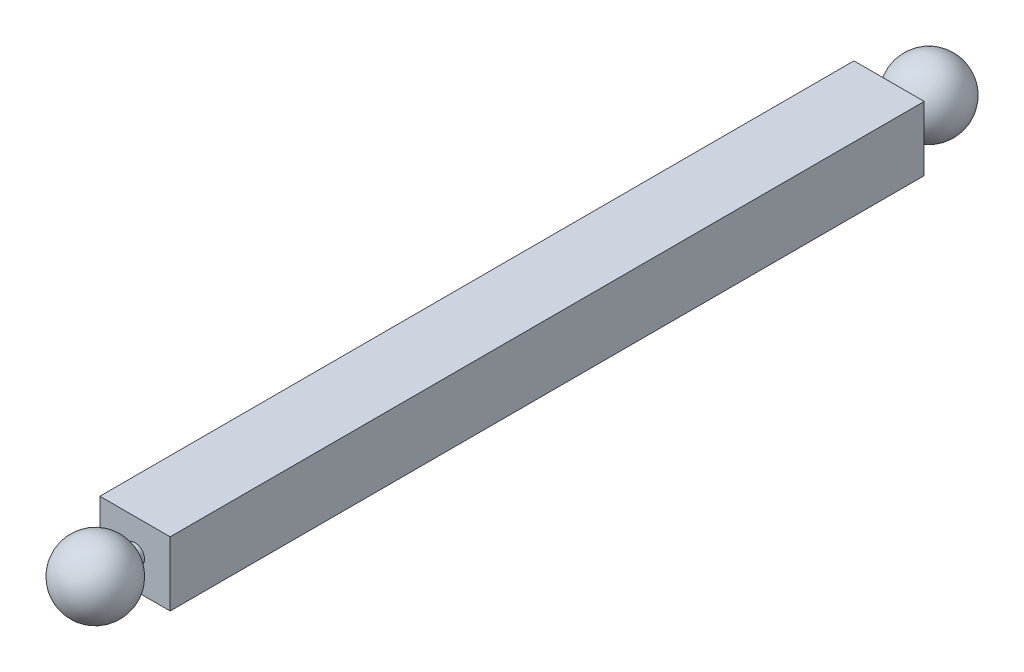
SolidWorks part; units mm, degrees
ref_plane "前视基准面" through (0, 0, 0) normal (0, 0, 1) x (1, 0, 0)
ref_plane "上视基准面" through (0, 0, 0) normal (0, 1, 0) x (1, 0, 0)
ref_plane "右视基准面" through (0, 0, 0) normal (1, 0, 0) x (0, 0, -1)
sketch "草图1" plane through (0, 0, 0) normal (0, 0, 1) x (1, 0, 0)
  line L0 (-8.5103, -3.5207) -> (-12.5103, -7.5207)
  line L1 (-12.5103, -3.5207) -> (-8.5103, -3.5207)
  line L2 (-12.5103, -3.5207) -> (-12.5103, -7.5207)
  line L3 (-12.5103, -7.5207) -> (-8.5103, -7.5207)
  line L4 (-8.5103, -3.5207) -> (-8.5103, -7.5207)
  line L5 (-12.5103, -3.5207) -> (-8.5103, -7.5207)
  circle A0 centre (-10.5103, -5.5207) radius 1.2
extrude "凸台-拉伸1" add sketch "草图1" along normal blind 5 contours L0 A0 L5 | L5 A0 L0 | L0 A0 L5 | L5 A0 L0
sketch "草图2" plane through (0, 0, 5) normal (0, 0, 1) x (1, 0, 0)
  line L0 (-7.2642, -2.5504) -> (-13.7563, -8.4911)
  line L1 (-10.5103, -5.5207) -> (-10.2831, -5.7479)
  arc A1 (-7.2642, -2.5504) -> (-13.7563, -8.4911) centre (-10.5103, -5.5207) cw
revolve "旋转2" add sketch "草图2" angle 360 about L0
sketch "草图3" plane through (0, 0, 0) normal (0, 0, -1) x (-1, 0, 0)
  line L0 (7.2642, -2.5504) -> (13.7563, -8.4911) construction
  line L1 (6.0844, -1.4707) -> (14.9362, -1.4707)
  line L2 (6.0844, -1.4707) -> (6.0844, -9.5708)
  line L3 (6.0844, -9.5708) -> (14.9362, -9.5708)
  line L4 (14.9362, -1.4707) -> (14.9362, -9.5708)
  line L5 (6.0844, -1.4707) -> (14.9362, -9.5708) construction
  line L6 (6.0844, -9.5708) -> (14.9362, -1.4707) construction
  point P0 (10.5103, -5.5207)
extrude "凸台-拉伸2" add sketch "草图3" along normal blind 95
sketch "草图4" plane through (0, -9.5708, 0) normal (0, -1, 0) x (-1, 0, 0)
  line L1 (6.0844, 95) -> (14.9362, 95) construction
  line L2 (12.2686, 99.4121) -> (11.9857, 98.718)
  line L3 (5.7608, 95) -> (6.5103, 95)
  arc A1 (6.5103, 95) -> (11.9857, 98.718) centre (10.5103, 95) ccw
  arc A2 (5.7608, 95) -> (12.2686, 99.4121) centre (10.5103, 95) ccw
  circle A3 centre (10.5103, 95) radius 4
sketch "草图7" plane through (0, 0, -95) normal (0, 0, -1) x (-1, 0, 0)
  circle A0 centre (10.5103, -5.5207) radius 0.8
extrude "凸台-拉伸3" add sketch "草图7" along normal blind 5
sketch "草图5" plane through (0, 0, -100) normal (0, 0, -1) x (-1, 0, 0)
  line L0 (13.7563, -2.5504) -> (7.2642, -8.4911)
  line L1 (10.0917, -4.6297) -> (10.3189, -4.8569)
  arc A0 (13.7563, -2.5504) -> (7.2642, -8.4911) centre (10.5103, -5.5207) cw
  point P5 (10.5103, -5.5207)
revolve "旋转4" add sketch "草图5" angle 360 about L0
